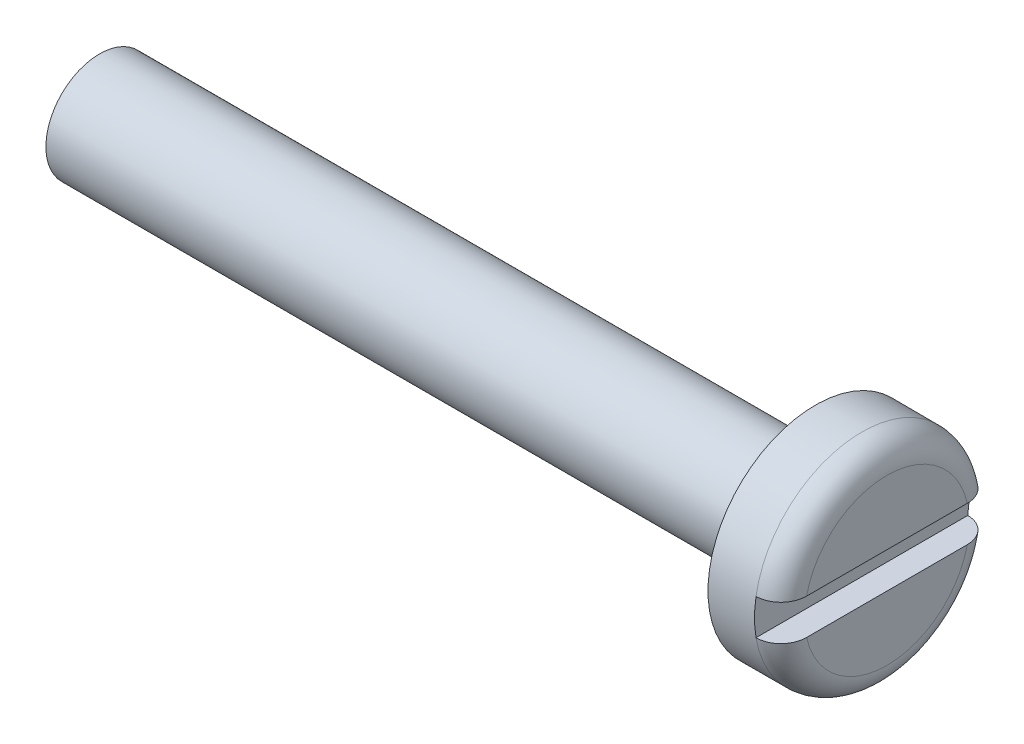
SolidWorks part; units mm, degrees
ref_plane "Piano frontale" through (0, 0, 0) normal (0, 0, 1) x (1, 0, 0)
ref_plane "Piano superiore" through (0, 0, 0) normal (0, 1, 0) x (1, 0, 0)
ref_plane "Piano destro" through (0, 0, 0) normal (1, 0, 0) x (0, 0, -1)
sketch "Schizzo1" plane through (0, 0, 0) normal (0, 0, 1) x (1, 0, 0)
  line L0 (0, 0) -> (-42.9072, 0) construction
  line L1 (0, 0) -> (-20, 0)
  dimension "D1" = 20
revolve "Rivoluzione-Sottile1" add sketch "Schizzo1" angle 360 about L0 wall 1.5
sketch "Schizzo3" plane through (0, 0, 0) normal (1, 0, 0) x (0, 0, -1)
  circle A0 centre (0, 0) radius 3
  dimension "D1" = 6
extrude "Estrusione-Estrusione1" add sketch "Schizzo3" along normal blind 2
sketch "Schizzo4" plane through (2, 0, 0) normal (1, 0, 0) x (0, 0, -1)
  line L1 (3.5, -0.5) -> (-3.5, -0.5)
  line L2 (3.5, -0.5) -> (3.5, 0.5)
  line L3 (3.5, 0.5) -> (-3.5, 0.5)
  line L4 (-3.5, -0.5) -> (-3.5, 0.5)
  line L5 (3.5, -0.5) -> (-3.5, 0.5) construction
  line L6 (3.5, 0.5) -> (-3.5, -0.5) construction
  point P0 (0, 0)
  dimension "D1" = 1
  dimension "D2" = 7
extrude "Taglio-Estrusione1" cut sketch "Schizzo4" against normal blind 0.7
fillet "Raccordo1" radius 0.7 2 edges at (2, -3, 0) (2, 3, 0)
